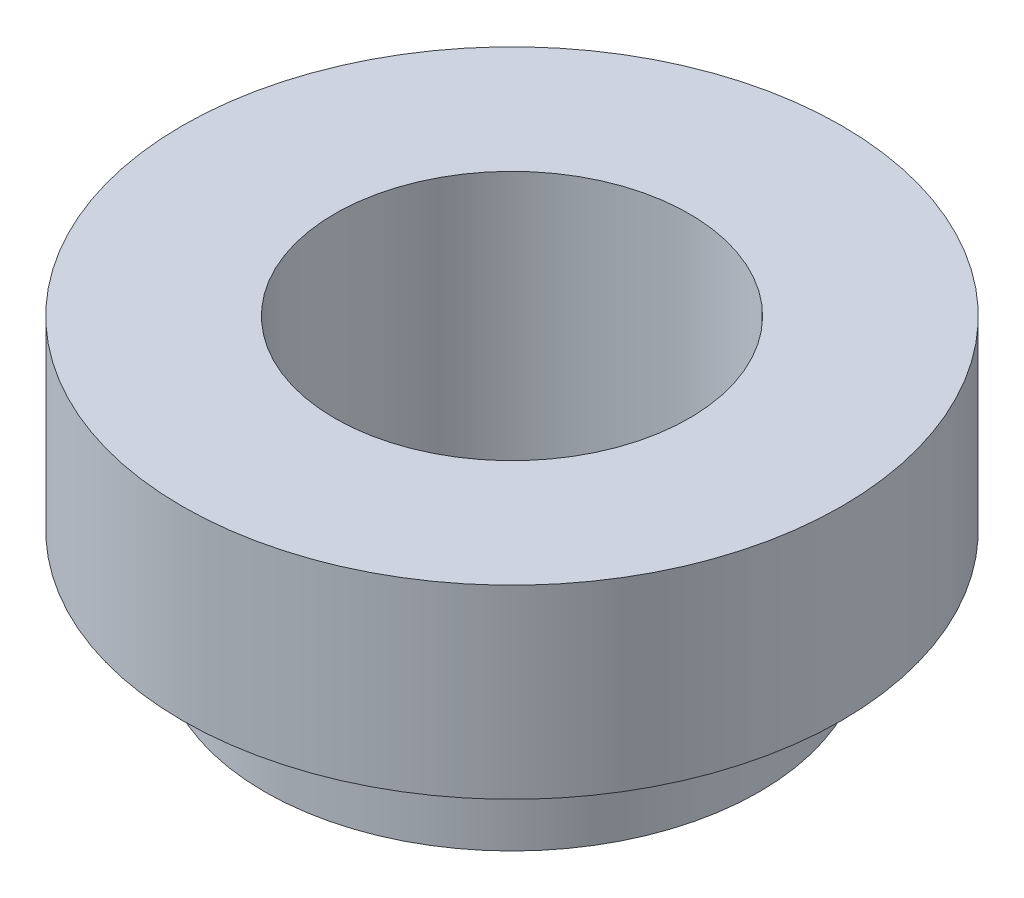
SolidWorks part; units mm, degrees
material "Nylon 101"
ref_plane "Front Plane" through (0, 0, 0) normal (0, 0, 1) x (1, 0, 0)
ref_plane "Top Plane" through (0, 0, 0) normal (0, 1, 0) x (1, 0, 0)
ref_plane "Right Plane" through (0, 0, 0) normal (1, 0, 0) x (0, 0, -1)
ref_axis "Axis1" through (0, -55, 0) along (0, 1, 0)
sketch "Sketch2" plane through (0, 0, 0) normal (0, 0, 1) x (1, 0, 0)
  line L0 (0, 0) -> (-8, 0)
  line L1 (-8, 0) -> (-8, -4.5)
  line L2 (-8, -4.5) -> (-6, -4.5)
  line L3 (-6, -4.5) -> (-6, -7)
  line L4 (-6, -7) -> (0, -7)
  line L5 (0, -55) -> (0, 55) construction
  line L6 (0, 0) -> (0, -7)
  dimension "D1" = 2.5
  dimension "D2" = 4.5
  dimension "D3" = 6
  dimension "D4" = 8
revolve "Revolve1" add sketch "Sketch2" angle 360 about axis through (0, -55, 0) along (0, 1, 0)
sketch "Sketch3" plane through (0, 0, 0) normal (0, 1, 0) x (1, 0, 0)
  circle A0 centre (0, 0) radius 4.3
  dimension "D1" = 8.6
extrude "Cut-Extrude1" cut sketch "Sketch3" against normal through all
